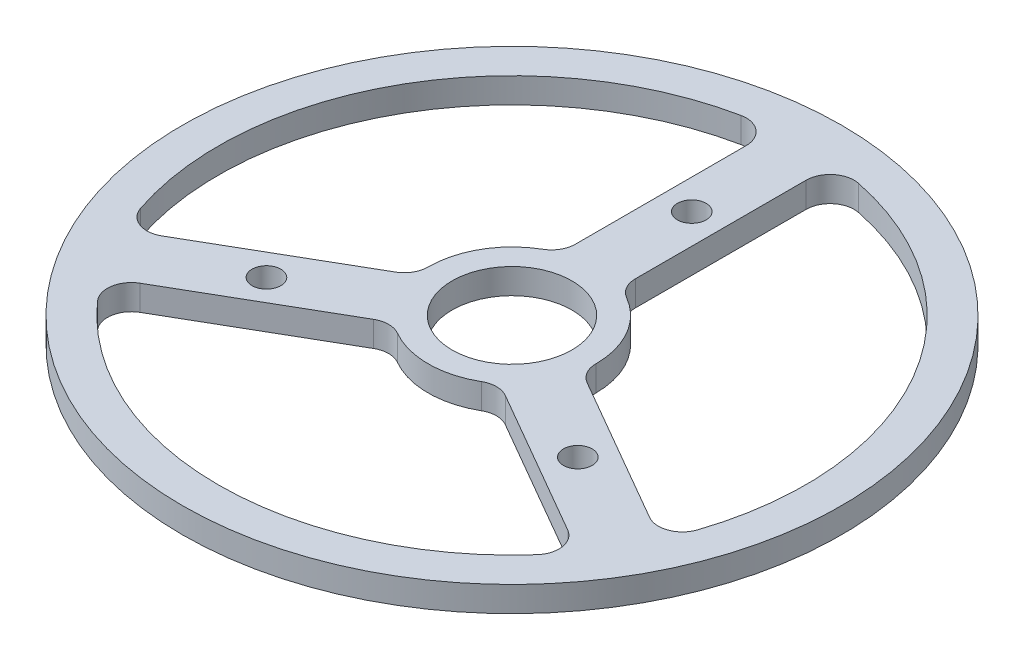
SolidWorks part; units mm, degrees
ref_plane "Alzado" through (0, 0, 0) normal (0, 0, 1) x (1, 0, 0)
ref_plane "Planta" through (0, 0, 0) normal (0, 1, 0) x (1, 0, 0)
ref_plane "Vista lateral" through (0, 0, 0) normal (1, 0, 0) x (0, 0, -1)
sketch "Croquis1" plane through (0, 0, 0) normal (0, 1, 0) x (1, 0, 0)
  circle A0 centre (0, 0) radius 27.5
  dimension "D1" = 55
extrude "Saliente-Extruir1" add sketch "Croquis1" along normal blind 2.11
sketch "Croquis2" plane through (0, 2.11, 0) normal (0, 1, 0) x (1, 0, 0)
  line L0 (0, -27.5) -> (0, 27.5) construction
  line L1 (-27.5, 0) -> (27.5, 0) construction
  line L11 (-2.5, 6.5383) -> (-2.5, 24.3721)
  line L13 (2.5, 6.5383) -> (2.5, 24.3721)
  line L18 (6.9124, -1.1041) -> (22.3569, -10.021)
  line L19 (4.4124, -5.4342) -> (19.8569, -14.3511)
  line L20 (-4.4124, -5.4342) -> (-19.8569, -14.3511)
  line L21 (-6.9124, -1.1041) -> (-22.3569, -10.021)
  circle A0 centre (0, 0) radius 27.5 construction
  circle A12 centre (0, 15) radius 1.2
  circle A13 centre (0, 0) radius 15 construction
  circle A14 centre (12.9904, -7.5) radius 1.2
  circle A15 centre (-12.9904, -7.5) radius 1.2
  circle A20 centre (0, 0) radius 5
  arc A21 (-2.5, 24.3721) -> (-22.3569, -10.021) centre (0, 0) ccw
  circle A22 centre (0, 0) radius 27.5 construction
  arc A23 (-2.5, 6.5383) -> (-6.9124, -1.1041) centre (0, 0) ccw
  arc A24 (6.9124, -1.1041) -> (2.5, 6.5383) centre (0, 0) ccw
  arc A25 (-4.4124, -5.4342) -> (4.4124, -5.4342) centre (0, 0) ccw
  arc A26 (22.3569, -10.021) -> (2.5, 24.3721) centre (0, 0) ccw
  arc A27 (-19.8569, -14.3511) -> (19.8569, -14.3511) centre (0, 0) ccw
  point P22 (0, 0)
  point P35 (0, 0)
  point P37 (0, 0)
  dimension "D1" = 3
  dimension "D2" = 10
  dimension "D6" = 30
  dimension "D5" = 2.4
  dimension "D4" = 14
  dimension "D3" = 5
  dimension "D8" = 3
  dimension "D7" = 3
extrude "Cortar-Extruir1" cut sketch "Croquis2" against normal through all
fillet "Redondeo1" radius 2 12 edges at (-4.4124, 1.055, 5.4342) (4.4124, 1.055, 5.4342) (6.9124, 1.055, 1.1041) (2.5, 1.055, -6.5383) (-6.9124, 1.055, 1.1041) (-2.5, 1.055, -6.5383) (-22.3569, 1.055, 10.021) (-19.8569, 1.055, 14.3511) (19.8569, 1.055, 14.3511) (22.3569, 1.055, 10.021) (-2.5, 1.055, -24.3721) (2.5, 1.055, -24.3721)
